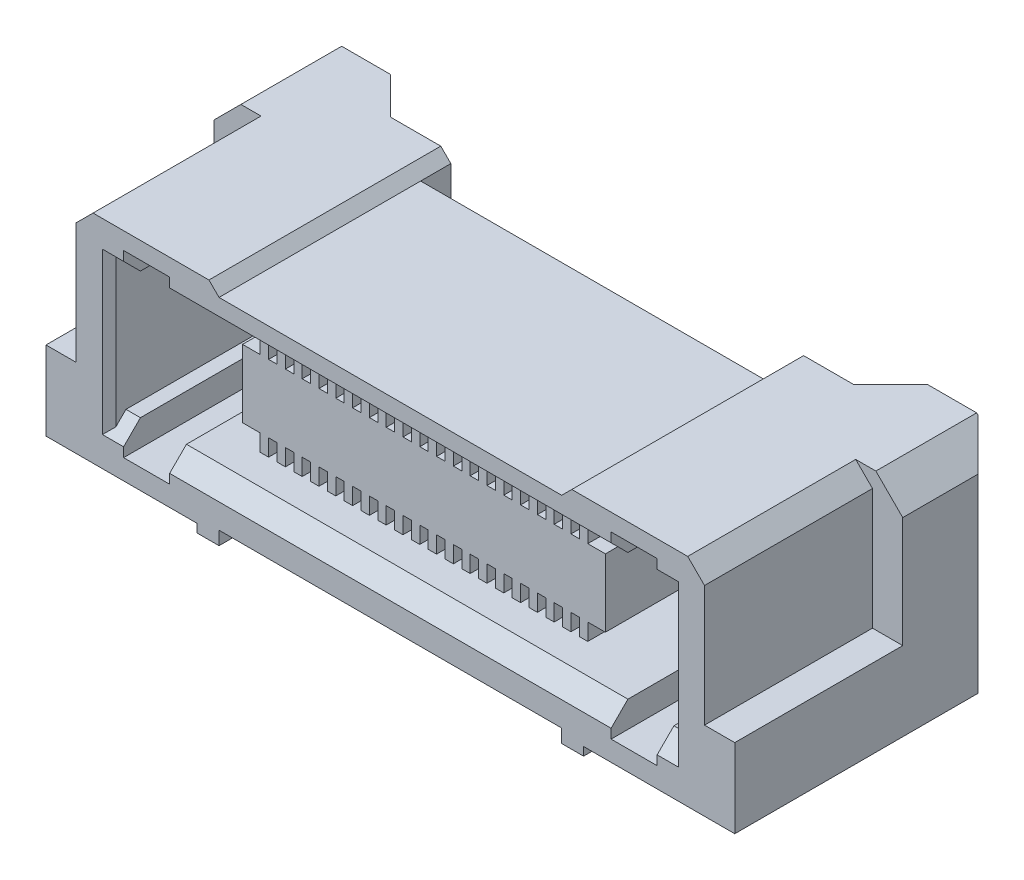
SolidWorks part; units mm, degrees
ref_plane "Спереди" through (0, 0, 0) normal (0, 0, 1) x (1, 0, 0)
ref_plane "Сверху" through (0, 0, 0) normal (0, 1, 0) x (1, 0, 0)
ref_plane "Справа" through (0, 0, 0) normal (1, 0, 0) x (0, 0, -1)
sketch "Эскиз1" plane through (0, 0, 0) normal (0, 0, 1) x (1, 0, 0)
  line L0 (557.5894, 82.7062) -> (585.2508, 82.7062) construction
  line L1 (5.1, 0) -> (-5.1, 0)
  line L2 (-5.1, 0) -> (-5.1, -0.4)
  line L3 (-5.1, -0.4) -> (-5.75, -0.4)
  line L4 (-5.75, -0.4) -> (-5.75, -0.15)
  line L5 (-5.75, -0.15) -> (-10.25, -0.15)
  line L6 (-10.25, -0.15) -> (-10.25, 5.5)
  line L7 (-10.25, 5.5) -> (-9.45, 6.3)
  line L8 (-9.45, 6.3) -> (-5.4, 6.3)
  line L9 (-5.4, 6.3) -> (-5.1, 6)
  line L10 (-5.1, 6) -> (5.1, 6)
  line L11 (0, 0) -> (0, 6) construction
  line L12 (5.4, 6.3) -> (5.1, 6)
  line L13 (9.45, 6.3) -> (5.4, 6.3)
  line L14 (10.25, 5.5) -> (9.45, 6.3)
  line L15 (10.25, -0.15) -> (10.25, 5.5)
  line L16 (5.75, -0.15) -> (10.25, -0.15)
  line L17 (5.75, -0.4) -> (5.75, -0.15)
  line L18 (5.1, -0.4) -> (5.75, -0.4)
  line L19 (5.1, 0) -> (5.1, -0.4)
  point P14 (10.0498, -1)
  dimension "D1" = 7.3
  dimension "D2" = 0.4
  dimension "D3" = 0.15
  dimension "D4" = 0.65
  dimension "D5" = 4.5
  dimension "D6" = 0.8
  dimension "D7" = 0.3
  dimension "D8" = 5.15
  dimension "D9" = 10.25
  dimension "D10" = 6
  dimension "D11" = 45
extrude "Бобышка-Вытянуть1" add sketch "Эскиз1" along normal blind 8
sketch "Эскиз2" plane through (0, 6.3, 0) normal (0, 1, 0) x (1, 0, 0)
  line L0 (184.2908, 122.8132) -> (963.6241, 122.8132) construction
  line L1 (-10.25, -0.76) -> (-9.49, 0)
  line L2 (-10.25, -8) -> (-10.25, 0) construction
  line L3 (-9.45, 0) -> (-10.25, 0) construction
  line L4 (-9.49, 0) -> (-8, 0)
  line L5 (-5.4, 0) -> (-9.45, 0) construction
  line L6 (-8, 0) -> (-6.9, -1.1)
  line L7 (-6.9, -1.1) -> (-5.1, -1.1)
  line L8 (-5.1, -8) -> (-5.1, 0) construction
  line L9 (-5.1, -1.1) -> (-5.1, -2)
  line L10 (-5.1, -2) -> (5.1, -2)
  line L11 (0, -2) -> (0, 0) construction
  line L12 (0, 0) -> (0, 1.9702) construction
  line L13 (10.25, 1.9702) -> (-10.25, 1.9702)
  line L14 (-10.25, 1.9702) -> (-10.25, -0.76)
  line L15 (10.25, 1.9702) -> (10.25, -0.76)
  line L16 (5.1, -1.1) -> (5.1, -2)
  line L17 (6.9, -1.1) -> (5.1, -1.1)
  line L18 (8, 0) -> (6.9, -1.1)
  line L19 (9.49, 0) -> (8, 0)
  line L20 (10.25, -0.76) -> (9.49, 0)
  line L21 (5.1, 0) -> (-5.1, 0) construction
  dimension "D1" = 1.1
  dimension "D2" = 0.76
  dimension "D3" = 45
  dimension "D4" = 3.35
  dimension "D5" = 2
extrude "Вырез-Вытянуть1" cut sketch "Эскиз2" against normal through all
sketch "Эскиз3" plane through (0, 0, 8) normal (0, 0, 1) x (1, 0, 0)
  line L0 (-10.25, 2.2) -> (-9.35, 2.2)
  line L1 (-10.25, -0.15) -> (-10.25, 5.5) construction
  line L2 (-9.35, 2.2) -> (-9.35, 5.8)
  line L3 (-9.35, 5.8) -> (-8.85, 6.3)
  line L4 (-9.45, 6.3) -> (-5.4, 6.3) construction
  line L5 (-8.85, 6.3) -> (-9.45, 6.3)
  line L6 (-9.45, 6.3) -> (-10.25, 5.5)
  line L7 (-10.25, 5.5) -> (-10.25, 2.2)
  line L8 (-5.75, -0.15) -> (-10.25, -0.15) construction
  line L9 (0, 0) -> (0, 6) construction
  line L10 (-5.1, 0) -> (5.1, 0) construction
  line L11 (5.1, 6) -> (-5.1, 6) construction
  line L12 (10.25, 5.5) -> (10.25, 2.2)
  line L13 (9.45, 6.3) -> (10.25, 5.5)
  line L14 (8.85, 6.3) -> (9.45, 6.3)
  line L15 (9.35, 5.8) -> (8.85, 6.3)
  line L16 (9.35, 2.2) -> (9.35, 5.8)
  line L17 (10.25, 2.2) -> (9.35, 2.2)
  dimension "D1" = 2.35
  dimension "D2" = 0.9
  dimension "D3" = 0.5
extrude "Вырез-Вытянуть2" cut sketch "Эскиз3" against normal blind 5
sketch "Эскиз4" plane through (0, 0, 8) normal (0, 0, 1) x (1, 0, 0)
sketch "Эскиз5" plane through (0, 0, 8) normal (0, 0, 1) x (1, 0, 0)
  line L0 (-8.37, 1.23) -> (-7.94, 1.23)
  line L1 (-7.94, 1.23) -> (-7.94, 0.45)
  line L2 (-7.94, 0.45) -> (-6.57, 0.45)
  line L3 (-6.57, 0.45) -> (-6.57, 1.23)
  line L4 (-6.57, 1.23) -> (6.57, 1.23)
  line L5 (0, 0) -> (0, 6) construction
  line L6 (-8.37, 1.23) -> (-8.37, 5.01)
  line L7 (-8.37, 5.01) -> (-7.94, 5.01)
  line L8 (-7.94, 5.01) -> (-7.94, 5.79)
  line L9 (-7.94, 5.79) -> (-6.57, 5.79)
  line L10 (-6.57, 5.79) -> (-6.57, 5.01)
  line L11 (-6.57, 5.01) -> (6.57, 5.01)
  line L12 (0, 5.01) -> (0, 1.23) construction
  line L13 (-5.1, 6) -> (5.1, 6) construction
  line L14 (6.57, 5.79) -> (6.57, 5.01)
  line L15 (7.94, 5.79) -> (6.57, 5.79)
  line L16 (7.94, 5.01) -> (7.94, 5.79)
  line L17 (8.37, 5.01) -> (7.94, 5.01)
  line L18 (8.37, 1.23) -> (8.37, 5.01)
  line L19 (6.57, 0.45) -> (6.57, 1.23)
  line L20 (7.94, 0.45) -> (6.57, 0.45)
  line L21 (7.94, 1.23) -> (7.94, 0.45)
  line L22 (8.37, 1.23) -> (7.94, 1.23)
  dimension "D1" = 3.78
  dimension "D2" = 8.37
  dimension "D3" = 0.78
  dimension "D4" = 0.43
  dimension "D5" = 1.37
  dimension "D6" = 0.99
extrude "Вырез-Вытянуть3" cut sketch "Эскиз5" against normal blind 5
sketch "Эскиз6" plane through (0, 0, 3) normal (0, 0, 1) x (1, 0, 0)
  line L0 (-5.4, 4.1402) -> (-5.4, 2.12)
  line L1 (-5.4, 2.12) -> (-4.875, 2.12)
  line L2 (-4.875, 2.12) -> (-4.875, 1.62)
  line L3 (-4.875, 1.62) -> (-4.625, 1.62)
  line L4 (-4.625, 1.62) -> (-4.625, 2.12)
  line L5 (-4.625, 2.12) -> (-4.375, 2.12)
  line L6 (-4.375, 2.12) -> (-4.375, 1.62)
  line L7 (-4.125, 1.62) -> (-4.125, 2.12)
  line L8 (-4.375, 1.62) -> (-4.125, 1.62)
  line L9 (-4.125, 2.12) -> (-3.875, 2.12)
  line L10 (-3.875, 2.12) -> (-3.875, 1.62)
  line L11 (-3.625, 1.62) -> (-3.625, 2.12)
  line L12 (-3.875, 1.62) -> (-3.625, 1.62)
  line L13 (-3.625, 2.12) -> (-3.375, 2.12)
  line L14 (-3.375, 2.12) -> (-3.375, 1.62)
  line L15 (-3.125, 1.62) -> (-3.125, 2.12)
  line L16 (-3.375, 1.62) -> (-3.125, 1.62)
  line L17 (-3.125, 2.12) -> (-2.875, 2.12)
  line L18 (-2.875, 2.12) -> (-2.875, 1.62)
  line L19 (-2.625, 1.62) -> (-2.625, 2.12)
  line L20 (-2.875, 1.62) -> (-2.625, 1.62)
  line L21 (-2.625, 2.12) -> (-2.375, 2.12)
  line L22 (-2.375, 2.12) -> (-2.375, 1.62)
  line L23 (-2.125, 1.62) -> (-2.125, 2.12)
  line L24 (-2.375, 1.62) -> (-2.125, 1.62)
  line L25 (-2.125, 2.12) -> (-1.875, 2.12)
  line L26 (-1.875, 2.12) -> (-1.875, 1.62)
  line L27 (-1.625, 1.62) -> (-1.625, 2.12)
  line L28 (-1.875, 1.62) -> (-1.625, 1.62)
  line L29 (-1.625, 2.12) -> (-1.375, 2.12)
  line L30 (-1.375, 2.12) -> (-1.375, 1.62)
  line L31 (-1.125, 1.62) -> (-1.125, 2.12)
  line L32 (-1.375, 1.62) -> (-1.125, 1.62)
  line L33 (-1.125, 2.12) -> (-0.875, 2.12)
  line L34 (-0.875, 2.12) -> (-0.875, 1.62)
  line L35 (-0.625, 1.62) -> (-0.625, 2.12)
  line L36 (-0.875, 1.62) -> (-0.625, 1.62)
  line L37 (-0.625, 2.12) -> (-0.375, 2.12)
  line L38 (-0.375, 2.12) -> (-0.375, 1.62)
  line L39 (-0.125, 1.62) -> (-0.125, 2.12)
  line L40 (-0.375, 1.62) -> (-0.125, 1.62)
  line L41 (-0.125, 2.12) -> (0.125, 2.12)
  line L42 (0.125, 2.12) -> (0.125, 1.62)
  line L43 (0.375, 1.62) -> (0.375, 2.12)
  line L44 (0.125, 1.62) -> (0.375, 1.62)
  line L45 (0.375, 2.12) -> (0.625, 2.12)
  line L46 (0.625, 2.12) -> (0.625, 1.62)
  line L47 (0.875, 1.62) -> (0.875, 2.12)
  line L48 (0.625, 1.62) -> (0.875, 1.62)
  line L49 (0.875, 2.12) -> (1.125, 2.12)
  line L50 (1.125, 2.12) -> (1.125, 1.62)
  line L51 (1.375, 1.62) -> (1.375, 2.12)
  line L52 (1.125, 1.62) -> (1.375, 1.62)
  line L53 (1.375, 2.12) -> (1.625, 2.12)
  line L54 (1.625, 2.12) -> (1.625, 1.62)
  line L55 (1.875, 1.62) -> (1.875, 2.12)
  line L56 (1.625, 1.62) -> (1.875, 1.62)
  line L57 (1.875, 2.12) -> (2.125, 2.12)
  line L58 (2.125, 2.12) -> (2.125, 1.62)
  line L59 (2.375, 1.62) -> (2.375, 2.12)
  line L60 (2.125, 1.62) -> (2.375, 1.62)
  line L61 (2.375, 2.12) -> (2.625, 2.12)
  line L62 (2.625, 2.12) -> (2.625, 1.62)
  line L63 (2.875, 1.62) -> (2.875, 2.12)
  line L64 (2.625, 1.62) -> (2.875, 1.62)
  line L65 (2.875, 2.12) -> (3.125, 2.12)
  line L66 (3.125, 2.12) -> (3.125, 1.62)
  line L67 (3.375, 1.62) -> (3.375, 2.12)
  line L68 (3.125, 1.62) -> (3.375, 1.62)
  line L69 (3.375, 2.12) -> (3.625, 2.12)
  line L70 (3.625, 2.12) -> (3.625, 1.62)
  line L71 (3.875, 1.62) -> (3.875, 2.12)
  line L72 (3.625, 1.62) -> (3.875, 1.62)
  line L73 (3.875, 2.12) -> (4.125, 2.12)
  line L74 (4.125, 2.12) -> (4.125, 1.62)
  line L75 (4.375, 1.62) -> (4.375, 2.12)
  line L76 (4.125, 1.62) -> (4.375, 1.62)
  line L77 (4.375, 2.12) -> (4.625, 2.12)
  line L78 (4.625, 2.12) -> (4.625, 1.62)
  line L79 (4.875, 1.62) -> (4.875, 2.12)
  line L80 (4.625, 1.62) -> (4.875, 1.62)
  line L81 (5.4, 4.1402) -> (5.4, 2.12)
  line L82 (0, 0) -> (0, 6) construction
  line L83 (0, 0) -> (0, 6) construction
  line L84 (5.1, 0) -> (-5.1, 0) construction
  line L85 (-5.4, 3.1301) -> (0, 3.1301) construction
  line L86 (5.4, 2.12) -> (4.875, 2.12)
  line L87 (4.875, 2.12) -> (5.125, 2.12) [skipped]
  line L88 (0, 6.2602) -> (0, 0.2602) construction
  line L89 (5.4, 4.1402) -> (4.875, 4.1402)
  line L90 (4.625, 4.6402) -> (4.875, 4.6402)
  line L91 (4.875, 4.6402) -> (4.875, 4.1402)
  line L92 (4.625, 4.1402) -> (4.625, 4.6402)
  line L93 (4.375, 4.1402) -> (4.625, 4.1402)
  line L94 (4.125, 4.6402) -> (4.375, 4.6402)
  line L95 (4.375, 4.6402) -> (4.375, 4.1402)
  line L96 (4.125, 4.1402) -> (4.125, 4.6402)
  line L97 (3.875, 4.1402) -> (4.125, 4.1402)
  line L98 (3.625, 4.6402) -> (3.875, 4.6402)
  line L99 (3.875, 4.6402) -> (3.875, 4.1402)
  line L100 (3.625, 4.1402) -> (3.625, 4.6402)
  line L101 (3.375, 4.1402) -> (3.625, 4.1402)
  line L102 (3.125, 4.6402) -> (3.375, 4.6402)
  line L103 (3.375, 4.6402) -> (3.375, 4.1402)
  line L104 (3.125, 4.1402) -> (3.125, 4.6402)
  line L105 (2.875, 4.1402) -> (3.125, 4.1402)
  line L106 (2.625, 4.6402) -> (2.875, 4.6402)
  line L107 (2.875, 4.6402) -> (2.875, 4.1402)
  line L108 (2.625, 4.1402) -> (2.625, 4.6402)
  line L109 (2.375, 4.1402) -> (2.625, 4.1402)
  line L110 (2.125, 4.6402) -> (2.375, 4.6402)
  line L111 (2.375, 4.6402) -> (2.375, 4.1402)
  line L112 (2.125, 4.1402) -> (2.125, 4.6402)
  line L113 (1.875, 4.1402) -> (2.125, 4.1402)
  line L114 (1.625, 4.6402) -> (1.875, 4.6402)
  line L115 (1.875, 4.6402) -> (1.875, 4.1402)
  line L116 (1.625, 4.1402) -> (1.625, 4.6402)
  line L117 (1.375, 4.1402) -> (1.625, 4.1402)
  line L118 (1.125, 4.6402) -> (1.375, 4.6402)
  line L119 (1.375, 4.6402) -> (1.375, 4.1402)
  line L120 (1.125, 4.1402) -> (1.125, 4.6402)
  line L121 (0.875, 4.1402) -> (1.125, 4.1402)
  line L122 (0.625, 4.6402) -> (0.875, 4.6402)
  line L123 (0.875, 4.6402) -> (0.875, 4.1402)
  line L124 (0.625, 4.1402) -> (0.625, 4.6402)
  line L125 (0.375, 4.1402) -> (0.625, 4.1402)
  line L126 (0.125, 4.6402) -> (0.375, 4.6402)
  line L127 (0.375, 4.6402) -> (0.375, 4.1402)
  line L128 (0.125, 4.1402) -> (0.125, 4.6402)
  line L129 (-0.125, 4.1402) -> (0.125, 4.1402)
  line L130 (-0.375, 4.6402) -> (-0.125, 4.6402)
  line L131 (-0.125, 4.6402) -> (-0.125, 4.1402)
  line L132 (-0.375, 4.1402) -> (-0.375, 4.6402)
  line L133 (-0.625, 4.1402) -> (-0.375, 4.1402)
  line L134 (-0.875, 4.6402) -> (-0.625, 4.6402)
  line L135 (-0.625, 4.6402) -> (-0.625, 4.1402)
  line L136 (-0.875, 4.1402) -> (-0.875, 4.6402)
  line L137 (-1.125, 4.1402) -> (-0.875, 4.1402)
  line L138 (-1.375, 4.6402) -> (-1.125, 4.6402)
  line L139 (-1.125, 4.6402) -> (-1.125, 4.1402)
  line L140 (-1.375, 4.1402) -> (-1.375, 4.6402)
  line L141 (-1.625, 4.1402) -> (-1.375, 4.1402)
  line L142 (-1.875, 4.6402) -> (-1.625, 4.6402)
  line L143 (-1.625, 4.6402) -> (-1.625, 4.1402)
  line L144 (-1.875, 4.1402) -> (-1.875, 4.6402)
  line L145 (-2.125, 4.1402) -> (-1.875, 4.1402)
  line L146 (-2.375, 4.6402) -> (-2.125, 4.6402)
  line L147 (-2.125, 4.6402) -> (-2.125, 4.1402)
  line L148 (-2.375, 4.1402) -> (-2.375, 4.6402)
  line L149 (-2.625, 4.1402) -> (-2.375, 4.1402)
  line L150 (-2.875, 4.6402) -> (-2.625, 4.6402)
  line L151 (-2.625, 4.6402) -> (-2.625, 4.1402)
  line L152 (-2.875, 4.1402) -> (-2.875, 4.6402)
  line L153 (-3.125, 4.1402) -> (-2.875, 4.1402)
  line L154 (-3.375, 4.6402) -> (-3.125, 4.6402)
  line L155 (-3.125, 4.6402) -> (-3.125, 4.1402)
  line L156 (-3.375, 4.1402) -> (-3.375, 4.6402)
  line L157 (-3.625, 4.1402) -> (-3.375, 4.1402)
  line L158 (-3.875, 4.6402) -> (-3.625, 4.6402)
  line L159 (-3.625, 4.6402) -> (-3.625, 4.1402)
  line L160 (-3.875, 4.1402) -> (-3.875, 4.6402)
  line L161 (-4.125, 4.1402) -> (-3.875, 4.1402)
  line L162 (-4.375, 4.6402) -> (-4.125, 4.6402)
  line L163 (-4.125, 4.6402) -> (-4.125, 4.1402)
  line L164 (-4.375, 4.1402) -> (-4.375, 4.6402)
  line L165 (-4.625, 4.1402) -> (-4.375, 4.1402)
  line L166 (-4.625, 4.6402) -> (-4.625, 4.1402)
  line L167 (-4.875, 4.6402) -> (-4.625, 4.6402)
  line L168 (-4.875, 4.1402) -> (-4.875, 4.6402)
  line L169 (-5.4, 4.1402) -> (-4.875, 4.1402)
  point P6 (0, 2.12)
  point P178 (0, 4.1402)
  dimension "D1" = 0.5
  dimension "D2" = 0.5
  dimension "D3" = 0.25
  dimension "D5" = 2.12
  dimension "D6" = 10.8
  dimension "D4" = 20
extrude "Бобышка-Вытянуть2" add sketch "Эскиз6" along normal blind 4
chamfer "Фаска1" distance 0.5 angle 45 6 edges at (8.155, 5.01, 8) (8.155, 1.23, 8) (-8.155, 5.01, 8) (-8.155, 1.23, 8) (0, 5.01, 8) (0, 1.23, 8)
chamfer "Фаска2" distance 0.2 angle 45 2 edges at (8.37, 3.12, 8) (-8.37, 3.12, 8)
sketch "Эскиз7" plane through (-10.25, 0, 0) normal (-1, 0, 0) x (0, 0, 1)
  line L0 (46.9841, 136.7435) -> (96.9031, 136.7435) construction
  line L1 (0.4, -0.15) -> (0.4, -2.7215) construction
  line L2 (0.76, -0.15) -> (0, -0.15) construction
  line L3 (2.15, -0.15) -> (2.15, -2.7215) construction
  line L4 (8, -0.15) -> (1.1, -0.15) construction
  line L5 (6.8, -0.15) -> (6.8, -2.7215) construction
  line L6 (8, -0.15) -> (0.76, -0.15) construction
  point P15 (6.8218, -2.7215)
  dimension "D1" = 0.4
  dimension "D2" = 1.75
  dimension "D3" = 6.4
ref_plane "Плоскость4" through (0, 0, 0.4) normal (0, 0, 1) x (1, 0, 0)
ref_plane "Плоскость5" through (0, 0, 2.15) normal (0, 0, 1) x (1, 0, 0)
sketch "Эскиз8" plane through (0, 0, 0.4) normal (0, 0, 1) x (1, 0, 0)
  line L0 (-7.29, -0.15) -> (-6.79, -0.65)
  line L1 (-5.75, -0.15) -> (-10.25, -0.15) construction
  line L2 (-6.79, -0.65) -> (-6.79, -1.9222)
  line L3 (-6.79, -1.9222) -> (-6.603, -2.2807)
  line L4 (-6.603, -2.2807) -> (-6.603, -2.4)
  line L5 (-6.603, -2.4) -> (-6.197, -2.4)
  line L6 (-6.4, -2.4) -> (-6.4, -0.15) construction
  line L7 (-6.197, -2.2807) -> (-6.197, -2.4)
  line L8 (-6.01, -1.9222) -> (-6.197, -2.2807)
  line L9 (-6.01, -1.9222) -> (-6.01, -0.15)
  line L10 (-6.01, -0.15) -> (-7.29, -0.15)
  line L12 (0, 0) -> (0, 6) construction
  line L13 (6.4, -2.4) -> (6.4, -0.15) construction
  line L14 (6.01, -0.15) -> (7.29, -0.15)
  line L15 (6.01, -1.9222) -> (6.01, -0.15)
  line L16 (6.01, -1.9222) -> (6.197, -2.2807)
  line L17 (6.197, -2.2807) -> (6.197, -2.4)
  line L18 (6.603, -2.4) -> (6.197, -2.4)
  line L19 (6.603, -2.2807) -> (6.603, -2.4)
  line L20 (6.79, -1.9222) -> (6.603, -2.2807)
  line L21 (6.79, -0.65) -> (6.79, -1.9222)
  line L22 (7.29, -0.15) -> (6.79, -0.65)
  dimension "D1" = 0.78
  dimension "D2" = 6.4
  dimension "D3" = 45
  dimension "D4" = 0.5
  dimension "D5" = 2.25
extrude "Бобышка-Вытянуть3" add sketch "Эскиз8" along normal mid plane 0.15 separate body
